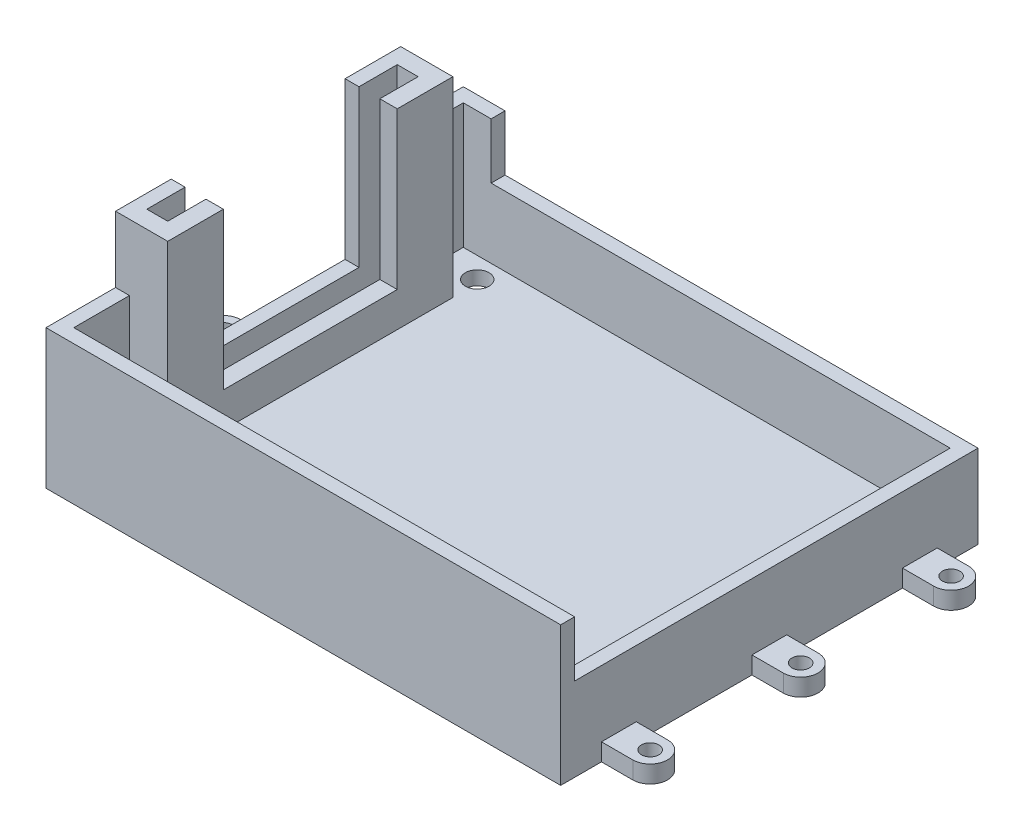
SolidWorks part; units mm, degrees
ref_plane "Piano frontale" through (0, 0, 0) normal (0, 0, 1) x (1, 0, 0)
ref_plane "Piano superiore" through (0, 0, 0) normal (0, 1, 0) x (1, 0, 0)
ref_plane "Piano destro" through (0, 0, 0) normal (1, 0, 0) x (0, 0, -1)
sketch "Schizzo1" plane through (0, 0, 0) normal (0, 1, 0) x (1, 0, 0)
  line L0 (0, 30) -> (0, -30) construction
  line L1 (-37, 30) -> (37, 30)
  line L2 (-37, 30) -> (-37, -30)
  line L3 (-37, -30) -> (37, -30)
  line L4 (37, 30) -> (37, -30)
  point P6 (0, 0)
  dimension "D1" = 74
  dimension "D2" = 60
extrude "Estrusione-Estrusione1" add sketch "Schizzo1" along normal blind 2
sketch "Schizzo2" plane through (0, 2, 0) normal (0, 1, 0) x (1, 0, 0)
  line L0 (-35, 28) -> (-35, -28)
  line L1 (-37, 30) -> (37, 30)
  line L2 (-37, 30) -> (-37, -30)
  line L3 (-37, -30) -> (37, -30)
  line L4 (37, 30) -> (37, -30)
  line L5 (-35, -28) -> (35, -28)
  line L6 (35, 28) -> (35, -28)
  line L7 (-35, 28) -> (35, 28)
  dimension "D1" = 2
extrude "Estrusione-Estrusione2" add sketch "Schizzo2" along normal blind 18 contours L2 L1 L4 L3 | L0 L5 L6 L7
sketch "Schizzo3" plane through (0, 0, 0) normal (0, -1, 0) x (1, 0, 0)
  line L0 (-37, -30) -> (-37, 30) construction
  line L1 (-37, 30) -> (37, 30) construction
  line L2 (0, -55) -> (0, 55) construction
  line L3 (55, 0) -> (-55, 0) construction
  circle A0 centre (-30, 25) radius 1.7
  circle A1 centre (30, 25) radius 1.7
  circle A2 centre (30, -25) radius 1.7
  circle A3 centre (-30, -25) radius 1.7
  dimension "D1" = 3.4
  dimension "D3" = 5
  dimension "D2" = 7
extrude "Taglio-Estrusione1" cut sketch "Schizzo3" against normal blind 8
sketch "Schizzo4" plane through (0, 0, -28) normal (0, 0, 1) x (1, 0, 0)
  line L1 (-31, 20) -> (37, 20)
  line L2 (-31, 20) -> (-31, 12)
  line L3 (-31, 12) -> (37, 12)
  line L4 (37, 20) -> (37, 12)
  dimension "D1" = 8
  dimension "D2" = 37
  dimension "D3" = 31
  dimension "D4" = 12
extrude "Taglio-Estrusione2" cut sketch "Schizzo4" along normal blind 56 and the other way blind 17
sketch "Schizzo5" plane through (0, 2, 0) normal (0, 1, 0) x (1, 0, 0)
  line L0 (-35, 28) -> (-35, -28) construction
  line L1 (-35, 21) -> (-29.5, 21)
  line L2 (-35, 21) -> (-35, 18.5)
  line L3 (-35, 18.5) -> (-32, 18.5)
  line L4 (-29.5, 21) -> (-29.5, 15.5697)
  line L5 (-29.5, -12) -> (-29.5, -6.7682)
  line L6 (-35, -17.5) -> (-32, -17.5)
  line L7 (-35, -17.5) -> (-35, -20)
  line L8 (-35, -20) -> (-29.5, -20)
  line L9 (-29.5, -6.7682) -> (-29.5, -20)
  line L11 (-29.5, 15.5697) -> (-29.5, 13)
  line L13 (-32, 18.5) -> (-32, 13)
  line L14 (-29.5, 13) -> (-32, 13)
  line L16 (-29.5, -12) -> (-32, -12)
  line L18 (-32, -12) -> (-32, -17.5)
  line L19 (-35, -28) -> (35, -28) construction
  point P12 (-32.25, 21)
  point P17 (-30.75, 13)
  line M13 (-35, 28) -> (-35, -28)
  dimension "D1" = 3
  dimension "D2" = 2.5
  dimension "D3" = 2.5
  dimension "D4" = 2.5
  dimension "D5" = 8
  dimension "D6" = 8
  dimension "D7" = 25
  dimension "D8" = 8
extrude "Estrusione-Estrusione3" add sketch "Schizzo5" along normal blind 27.5 contours L3 L13 L6 L11 | L9 L6 L8 M13
sketch "Schizzo6" plane through (0, 2, 0) normal (0, 1, 0) x (1, 0, 0)
  line L1 (-32, -12) -> (-29.5, -12)
  line L2 (-32, -12) -> (-32, 13)
  line L3 (-32, 13) -> (-29.5, 13)
  line L4 (-29.5, -12) -> (-29.5, 13)
extrude "Estrusione-Estrusione4" add sketch "Schizzo6" along normal blind 5
sketch "Schizzo7" plane through (-35, 0, 0) normal (1, 0, 0) x (0, 0, -1)
  line L1 (-12, 20) -> (13, 20)
  line L2 (-12, 20) -> (-12, 7)
  line L3 (-12, 7) -> (13, 7)
  line L4 (13, 20) -> (13, 7)
extrude "Taglio-Estrusione3" cut sketch "Schizzo7" against normal blind 5
sketch "Schizzo8" plane through (0, 20, 0) normal (0, 1, 0) x (1, 0, 0)
  line L1 (-35, 21) -> (-37, 21)
  line L2 (-35, 21) -> (-35, 13)
  line L3 (-35, 13) -> (-37, 13)
  line L4 (-37, 21) -> (-37, 13)
  line L5 (-35, -20) -> (-37, -20)
  line L6 (-35, -20) -> (-35, -12)
  line L7 (-35, -12) -> (-37, -12)
  line L8 (-37, -20) -> (-37, -12)
extrude "Estrusione-Estrusione5" add sketch "Schizzo8" along normal up to surface (9.5 mm away) up to face at (-32.1667, 29.5, -17.5)
sketch "Schizzo9" plane through (0, 0, 0) normal (0, -1, 0) x (1, 0, 0)
  line L0 (-37, 24.1366) -> (-41.5, 24.1366)
  line L1 (-37, -30) -> (-37, 30) construction
  line L2 (-37, 24.1366) -> (-37, 19.1366)
  line L3 (-41.5, 19.1366) -> (-37, 19.1366)
  line L4 (16.225, 0) -> (-16.225, 0) construction
  line L5 (-41.5, -19.1366) -> (-37, -19.1366)
  line L6 (-37, -24.1366) -> (-37, -19.1366)
  line L7 (-37, -24.1366) -> (-41.5, -24.1366)
  line L8 (0, -16.225) -> (0, 16.225) construction
  line L9 (37, -24.1366) -> (41.5, -24.1366)
  line L10 (37, -24.1366) -> (37, -19.1366)
  line L11 (41.5, -19.1366) -> (37, -19.1366)
  line L12 (41.5, 19.1366) -> (37, 19.1366)
  line L13 (37, 24.1366) -> (37, 19.1366)
  line L14 (37, 24.1366) -> (41.5, 24.1366)
  line L16 (-37, -2.5) -> (-41.5, -2.5)
  line L18 (-41.5, 2.5) -> (-37, 2.5)
  line L20 (-37, -2.5) -> (-37, 2.5)
  line L21 (37, -2.5) -> (37, 2.5)
  line L22 (41.5, 2.5) -> (37, 2.5)
  line L23 (37, -2.5) -> (41.5, -2.5)
  arc A0 (-41.5, 24.1366) -> (-41.5, 19.1366) centre (-41.5, 21.6366) ccw
  circle A1 centre (-41.5, 21.6366) radius 1.25
  circle A2 centre (-41.5, -21.6366) radius 1.25
  arc A3 (-41.5, -24.1366) -> (-41.5, -19.1366) centre (-41.5, -21.6366) cw
  arc A4 (41.5, -24.1366) -> (41.5, -19.1366) centre (41.5, -21.6366) ccw
  circle A5 centre (41.5, -21.6366) radius 1.25
  circle A6 centre (41.5, 21.6366) radius 1.25
  arc A7 (41.5, 24.1366) -> (41.5, 19.1366) centre (41.5, 21.6366) cw
  arc A8 (-41.5, 2.5) -> (-41.5, -2.5) centre (-41.5, 0) ccw
  circle A9 centre (-41.5, 0) radius 1.25
  circle A10 centre (41.5, 0) radius 1.25
  arc A11 (41.5, 2.5) -> (41.5, -2.5) centre (41.5, 0) cw
  point P30 (-37, 0)
  point P35 (-37, 0)
  line M15 (-37, 30) -> (-37, -30)
  line M17 (37, -30) -> (37, 30)
  dimension "D1" = 2.5
  dimension "D2" = 2.5
  dimension "D7" = 2.5
  dimension "D3" = 0
  dimension "D4" = 5
  dimension "D5" = 4.5
  dimension "D6" = 4.5
extrude "Estrusione-Estrusione6" add sketch "Schizzo9" against normal blind 2.5 contours A3 L7 L5 A2 M15 | L18 A8 L16 A9 M15 | L0 A0 L3 A1 M15 | A7 L14 L12 A6 M17 | A11 L22 L23 A10 M17 | L9 A4 L11 A5 M17
